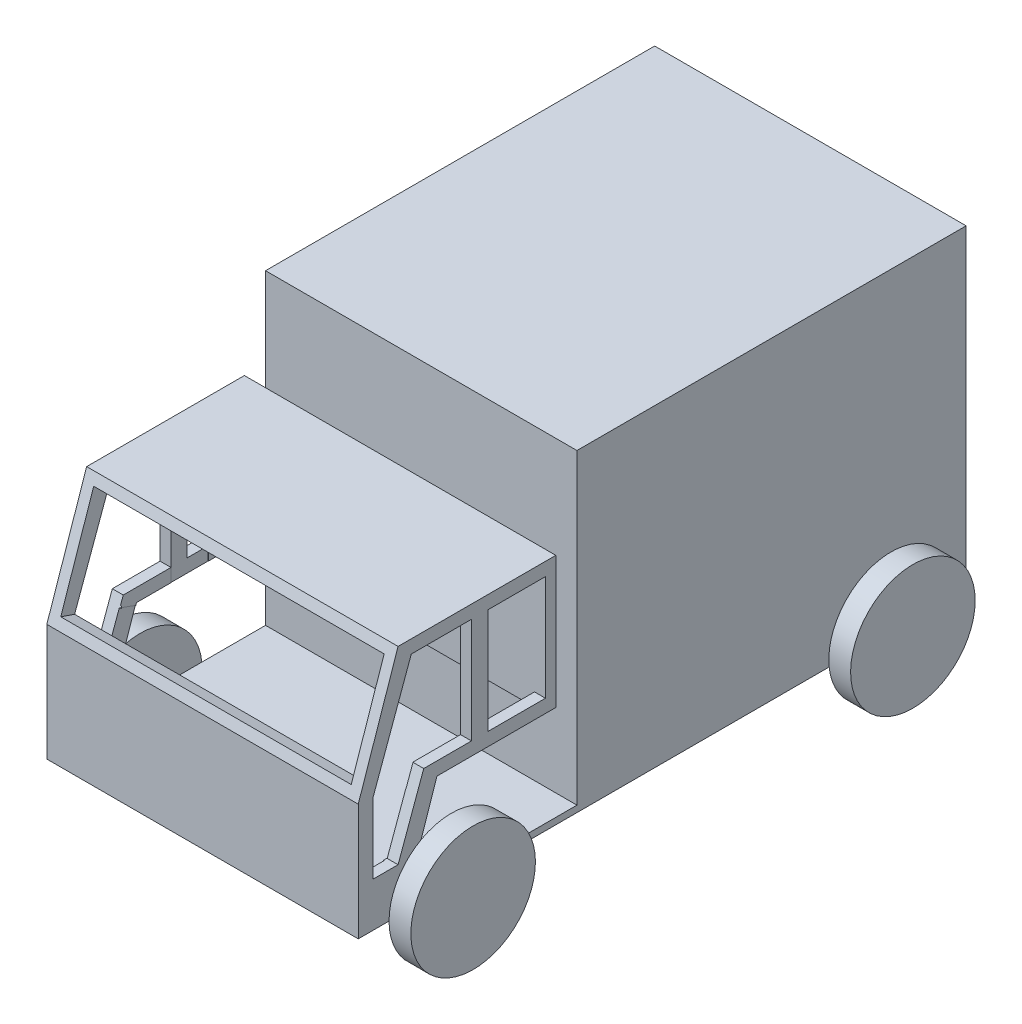
SolidWorks part; units mm, degrees
ref_plane "Front Plane" through (0, 0, 0) normal (0, 0, 1) x (1, 0, 0)
ref_plane "Top Plane" through (0, 0, 0) normal (0, 1, 0) x (1, 0, 0)
ref_plane "Right Plane" through (0, 0, 0) normal (1, 0, 0) x (0, 0, -1)
sketch "Çizim2" plane through (0, 0, 0) normal (1, 0, 0) x (0, 0, -1)
  line L0 (321.6737, 584.2021) -> (1241.5083, 591.8221) construction
  line L6 (1257.8367, 931.4533) -> (633.0024, 931.4533)
  line L7 (1257.8367, 931.4533) -> (1257.8367, 438.3349)
  line L8 (1257.8367, 438.3349) -> (633.0024, 438.3349)
  line L9 (633.0024, 931.4533) -> (633.0024, 438.3349)
extrude "Yükseklik-Ekstrüzyon1" add sketch "Çizim2" against normal blind 500
sketch "Çizim4" plane through (0, 0, 0) normal (1, 0, 0) x (0, 0, -1)
  line L0 (633.0024, 438.3349) -> (1257.8367, 438.3349) construction
  circle A0 centre (1137.3543, 438.3349) radius 100
extrude "Yükseklik-Ekstrüzyon2" add sketch "Çizim4" along normal blind 35
sketch "Çizim5" plane through (0, 0, 0) normal (1, 0, 0) x (0, 0, -1)
  line L1 (1257.8367, 438.3349) -> (281.8689, 438.3349)
  line L2 (1257.8367, 438.3349) -> (1257.8367, 427.9396)
  line L3 (1257.8367, 427.9396) -> (281.8689, 427.9396)
  line L4 (281.8689, 438.3349) -> (281.8689, 427.9396)
extrude "Yükseklik-Ekstrüzyon3" add sketch "Çizim5" against normal blind 500
sketch "Çizim6" plane through (0, 0, 0) normal (1, 0, 0) x (0, 0, -1)
  line L1 (281.8689, 427.9396) -> (599.0713, 427.9396)
  line L2 (281.8689, 427.9396) -> (281.8689, 802.644)
  line L3 (281.8689, 802.644) -> (599.0713, 802.644)
  line L4 (599.0713, 427.9396) -> (599.0713, 802.644)
extrude "Yükseklik-Ekstrüzyon4" add sketch "Çizim6" against normal blind 500
sketch "Çizim7" plane through (0, 0, 0) normal (1, 0, 0) x (0, 0, -1)
  line L0 (281.8689, 802.644) -> (345.8192, 802.644)
  line L1 (599.0713, 802.644) -> (281.8689, 802.644) construction
  line L2 (345.8192, 802.644) -> (281.8689, 615.2918)
  line L3 (281.8689, 802.644) -> (281.8689, 427.9396) construction
  line L4 (281.8689, 615.2918) -> (281.8689, 802.644)
extrude "Kes-Ekstrüzyon1" cut sketch "Çizim7" against normal blind 500
sketch "Çizim8" plane through (0, 0, 0) normal (1, 0, 0) x (0, 0, -1)
  line L0 (345.8192, 802.644) -> (367.0324, 781.4308) construction
  line L1 (367.0324, 781.4308) -> (305.4688, 612.2862)
  line L2 (305.4688, 612.2862) -> (305.4688, 499.1233)
  line L3 (305.4688, 499.1233) -> (345.8192, 499.1233)
  line L4 (345.8192, 499.1233) -> (387.0072, 612.2862)
  line L5 (387.0072, 612.2862) -> (582.3923, 612.2862)
  line L6 (582.3923, 612.2862) -> (582.3923, 781.4308)
  line L7 (582.3923, 781.4308) -> (367.0324, 781.4308)
extrude "Kes-Ekstrüzyon2" cut sketch "Çizim8" against normal blind 500
sketch "Çizim10" plane through (0, 0, 0) normal (1, 0, 0) x (0, 0, -1)
  line L0 (387.0072, 612.2862) -> (408.2204, 591.0729) construction
  line L1 (599.0713, 438.3349) -> (356.5412, 438.3349)
  line L2 (356.5412, 438.3349) -> (408.2204, 591.0729)
  line L3 (408.2204, 591.0729) -> (599.0713, 591.0729)
  line L4 (599.0713, 438.3349) -> (599.0713, 802.644) construction
  line L5 (599.0713, 591.0729) -> (599.0713, 438.3349)
extrude "Kes-Ekstrüzyon3" cut sketch "Çizim10" against normal blind 500
sketch "Çizim11" plane through (0, 0, 0) normal (1, 0, 0) x (0, 0, -1)
  line L0 (281.8689, 427.9396) -> (1037.8961, 427.9396) construction
  circle A0 centre (431.3213, 427.9396) radius 100
extrude "Yükseklik-Ekstrüzyon5" add sketch "Çizim11" along normal blind 35
sketch "Çizim12" plane through (0, -21.9648, -64.3494) normal (0, 0.323, 0.9464) x (1, 0, 0)
  line L0 (-500, 871.3238) -> (0, 673.3578) construction
  line L6 (-483.1517, 690.3914) -> (-16.8483, 690.3914)
  line L7 (-483.1517, 690.3914) -> (-483.1517, 854.2902)
  line L8 (-483.1517, 854.2902) -> (-16.8483, 854.2902)
  line L9 (-16.8483, 690.3914) -> (-16.8483, 854.2902)
  line L10 (-483.1517, 690.3914) -> (-16.8483, 854.2902) construction
  line L11 (-483.1517, 854.2902) -> (-16.8483, 690.3914) construction
  point P2 (-250, 772.3408)
extrude "Kes-Ekstrüzyon4" cut sketch "Çizim12" against normal blind 35
sketch "Çizim15" plane through (0, 802.644, 0) normal (0, 1, 0) x (1, 0, 0)
  line L1 (-500, 582.3923) -> (0, 582.3923)
  line L2 (-500, 582.3923) -> (-500, 382.565)
  line L3 (-500, 382.565) -> (0, 382.565)
  line L4 (0, 582.3923) -> (0, 382.565)
sketch "Çizim17" plane through (0, 612.2862, 0) normal (0, 1, 0) x (1, 0, 0)
  line L0 (-500, 582.3923) -> (0, 382.565) construction
  line L1 (-500, 582.3923) -> (0, 582.3923) construction
  line L2 (-482.4354, 382.565) -> (-17.5646, 382.565)
  line L3 (-482.4354, 382.565) -> (-482.4354, 582.3923)
  line L4 (-482.4354, 582.3923) -> (-17.5646, 582.3923)
  line L5 (-17.5646, 382.565) -> (-17.5646, 582.3923)
  line L6 (-482.4354, 382.565) -> (-17.5646, 582.3923) construction
  line L7 (-482.4354, 582.3923) -> (-17.5646, 382.565) construction
  point P4 (-250, 482.4786)
extrude "Kes-Ekstrüzyon7" cut sketch "Çizim17" against normal blind 35
sketch "Çizim20" plane through (0, -52.7578, -144.9509) normal (0, 0.342, 0.9397) x (1, 0, 0)
  line L1 (-483.1517, 691.6201) -> (-17.4913, 691.6201)
  line L2 (-483.1517, 691.6201) -> (-483.1517, 587.0287)
  line L3 (-483.1517, 587.0287) -> (-17.4913, 587.0287)
  line L4 (-17.4913, 691.6201) -> (-17.4913, 587.0287)
extrude "Kes-Ekstrüzyon8" cut sketch "Çizim20" against normal blind 35
sketch "Çizim21" plane through (0, -52.7578, -144.9509) normal (0, 0.342, 0.9397) x (1, 0, 0)
  line L0 (-500, 674.59) -> (0, 674.59) construction
  line L1 (-480.7848, 707.7483) -> (-17.2215, 707.7483)
  line L2 (-480.7848, 707.7483) -> (-480.7848, 674.59)
  line L3 (-480.7848, 674.59) -> (-17.2215, 674.59)
  line L4 (-17.2215, 707.7483) -> (-17.2215, 674.59)
extrude "Kes-Ekstrüzyon9" cut sketch "Çizim21" against normal blind 35
sketch "Çizim22" plane through (0, -63.2177, -186.8402) normal (0, -0.3205, -0.9472) x (-1, 0, 0)
  line L1 (17.9505, 583.6669) -> (483.7207, 583.6669)
  line L2 (17.9505, 583.6669) -> (17.9505, 527.9641)
  line L3 (17.9505, 527.9641) -> (483.7207, 527.9641)
  line L4 (483.7207, 583.6669) -> (483.7207, 527.9641)
extrude "Kes-Ekstrüzyon10" cut sketch "Çizim22" against normal blind 35
sketch "Çizim23" plane through (0, 499.1233, 0) normal (0, 1, 0) x (1, 0, 0)
  line L1 (-483.1517, 340.3168) -> (-16.8483, 340.3168)
  line L2 (-483.1517, 340.3168) -> (-483.1517, 309.6609)
  line L3 (-483.1517, 309.6609) -> (-16.8483, 309.6609)
  line L4 (-16.8483, 340.3168) -> (-16.8483, 309.6609)
extrude "Kes-Ekstrüzyon11" cut sketch "Çizim23" against normal blind 60
sketch "Çizim25" plane through (0, 0, 0) normal (1, 0, 0) x (0, 0, -1)
  line L0 (582.3923, 802.644) -> (382.565, 802.644) construction
  line L1 (463.6587, 802.644) -> (489.9327, 802.644)
  line L2 (463.6587, 802.644) -> (463.6587, 591.0729)
  line L3 (463.6587, 591.0729) -> (489.9327, 591.0729)
  line L4 (489.9327, 802.644) -> (489.9327, 591.0729)
  line L5 (599.0713, 591.0729) -> (408.2204, 591.0729) construction
extrude "Yükseklik-Ekstrüzyon6" add sketch "Çizim25" against normal blind 500
sketch "Çizim27" plane through (0, 0, -463.6587) normal (0, 0, 1) x (1, 0, 0)
  line L0 (-500, 708.9679) -> (-482.78, 708.9679) construction
  line L1 (-500, 615.2918) -> (-500, 802.644) construction
  line L2 (0, 702.4781) -> (-16.8483, 702.4781) construction
  line L3 (0, 615.2918) -> (0, 802.644) construction
  line L4 (-16.8483, 631.4122) -> (-16.8483, 786.5237) construction
  line L5 (-500, 781.4308) -> (0, 781.4308) construction
  line L6 (-482.78, 781.4308) -> (-17.5646, 781.4308)
  line L7 (-482.78, 781.4308) -> (-482.78, 591.0729)
  line L8 (-482.78, 591.0729) -> (-17.5646, 591.0729)
  line L9 (-17.5646, 781.4308) -> (-17.5646, 591.0729)
extrude "Kes-Ekstrüzyon12" cut sketch "Çizim27" against normal blind 60
sketch "Çizim28" plane through (-500, 0, 0) normal (-1, 0, 0) x (0, 0, 1)
  line L0 (-531.3213, 427.9396) -> (-331.3213, 427.9396) construction
  line L1 (-633.0024, 438.3349) -> (-1257.8367, 438.3349) construction
  line L2 (-1257.8367, 427.9396) -> (-1257.8367, 931.4533) construction
  line L3 (-1236.8125, 427.9396) -> (-1034.6148, 438.3349) construction
  line L4 (-1135.7136, 433.1372) -> (-1135.7136, 438.3349) construction
  circle A0 centre (-431.3213, 427.9396) radius 100
  circle A1 centre (-1135.7136, 438.3349) radius 100
extrude "Yükseklik-Ekstrüzyon7" add sketch "Çizim28" along normal blind 35
